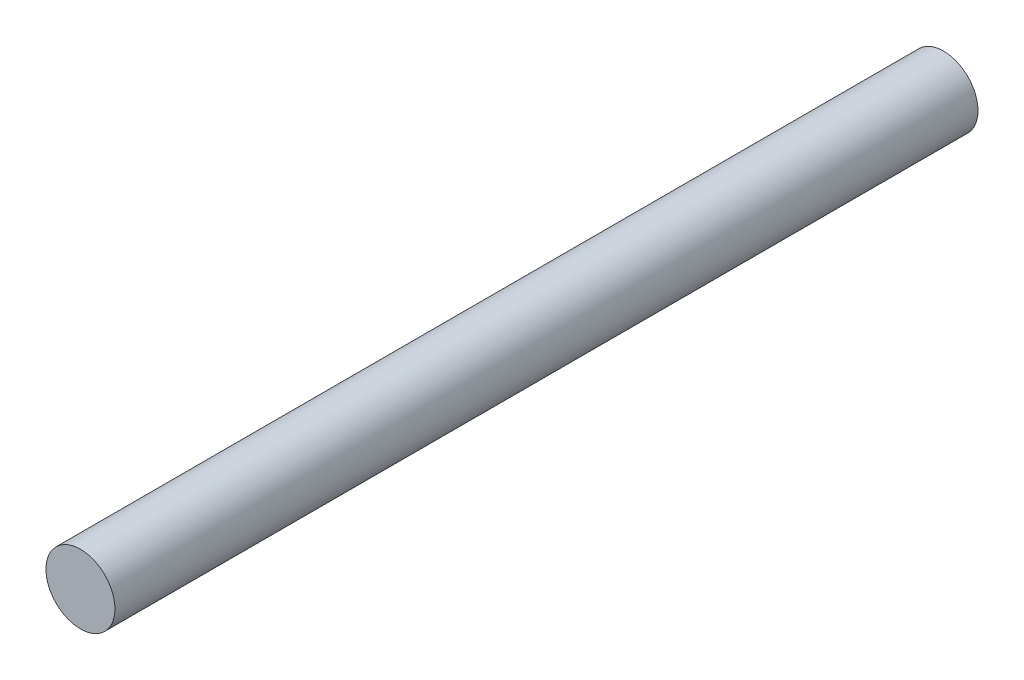
SolidWorks part; units mm, degrees
ref_plane "Front Plane" through (0, 0, 0) normal (0, 0, 1) x (1, 0, 0)
ref_plane "Top Plane" through (0, 0, 0) normal (0, 1, 0) x (1, 0, 0)
ref_plane "Right Plane" through (0, 0, 0) normal (1, 0, 0) x (0, 0, -1)
sketch "Sketch1" plane through (0, 0, 0) normal (0, 0, 1) x (1, 0, 0)
  circle A0 centre (0, 0) radius 25
  dimension "D1" = 50
extrude "Boss-Extrude1" add sketch "Sketch1" along normal blind 625
sketch "Sketch2" plane through (0, 0, 0) normal (0, 1, 0) x (1, 0, 0)
